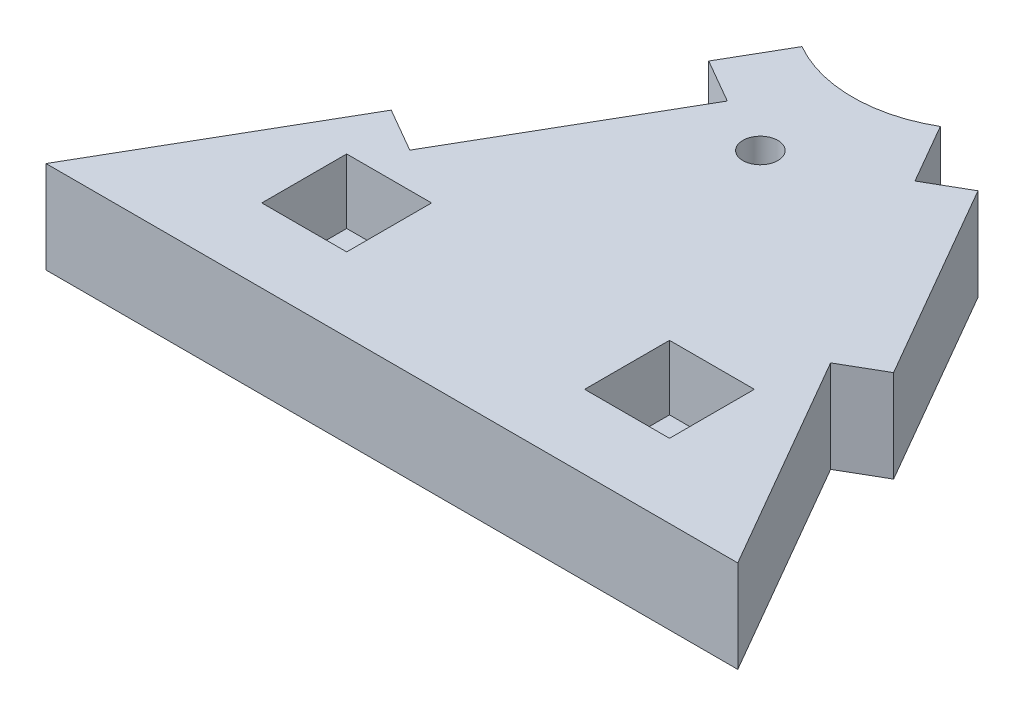
SolidWorks part; units mm, degrees
ref_plane "Front Plane" through (0, 0, 0) normal (0, 0, 1) x (1, 0, 0)
ref_plane "Top Plane" through (0, 0, 0) normal (0, 1, 0) x (1, 0, 0)
ref_plane "Right Plane" through (0, 0, 0) normal (1, 0, 0) x (0, 0, -1)
sketch "Sketch1" plane through (0, 0, 0) normal (0, 1, 0) x (1, 0, 0)
  line L0 (0, 0) -> (75, 0)
  line L1 (75, 0) -> (37.5, 64.9519)
  line L2 (37.5, 64.9519) -> (0, 0)
  dimension "D1" = 75
  dimension "D2" = 75
  dimension "D3" = 75
extrude "Boss-Extrude1" add sketch "Sketch1" along normal blind 10
sketch "Sketch2" plane through (0, 10, 0) normal (0, 1, 0) x (1, 0, 0)
  line L0 (37.5, 64.9519) -> (37.5, 0) construction
  line L1 (0, 0) -> (75, 0) construction
  line L2 (20, 0) -> (20, 34.641) construction
  line L6 (37.5, 64.9519) -> (0, 0) construction
  line L7 (50.4, 8) -> (50.4, 17.2)
  line L8 (15.4, 8) -> (24.6, 8)
  line L9 (15.4, 8) -> (15.4, 17.2)
  line L10 (15.4, 17.2) -> (24.6, 17.2)
  line L11 (24.6, 8) -> (24.6, 17.2)
  line L12 (15.4, 8) -> (24.6, 17.2) construction
  line L13 (15.4, 17.2) -> (24.6, 8) construction
  line L14 (59.6, 8) -> (50.4, 8)
  line L15 (59.6, 8) -> (59.6, 17.2)
  line L16 (59.6, 17.2) -> (50.4, 17.2)
  point P13 (20, 12.6)
  dimension "D1" = 17.5
  dimension "D3" = 8
  dimension "D4" = 9.2
  dimension "D5" = 9.2
extrude "Cut-Extrude1" cut sketch "Sketch2" against normal blind 7
sketch "Sketch3" plane through (0, 10, 0) normal (0, 1, 0) x (1, 0, 0)
  line L0 (18.75, 32.476) -> (26.3, 45.5529)
  line L1 (37.5, 64.9519) -> (0, 0) construction
  line L2 (26.3, 45.5529) -> (31.0631, 42.8029)
  line L3 (31.0631, 42.8029) -> (18.4631, 20.9791)
  line L4 (18.4631, 20.9791) -> (13.7, 23.7291)
  line L5 (13.7, 23.7291) -> (18.75, 32.476)
  dimension "D1" = 15.1
  dimension "D2" = 10.1
  dimension "D3" = 5.5
  dimension "D4" = 5.5
extrude "Cut-Extrude2" cut sketch "Sketch3" against normal through all
sketch "Sketch4" plane through (0, 10, 0) normal (0, 1, 0) x (1, 0, 0)
  line L0 (56.25, 32.476) -> (48.75, 45.4663)
  line L1 (75, 0) -> (37.5, 64.9519) construction
  line L2 (48.75, 45.4663) -> (53.0801, 47.9663)
  line L3 (53.0801, 47.9663) -> (65.5801, 26.3157)
  line L4 (65.5801, 26.3157) -> (61.25, 23.8157)
  line L5 (61.25, 23.8157) -> (56.25, 32.476)
  dimension "D1" = 15
  dimension "D2" = 10
  dimension "D3" = 5
  dimension "D4" = 5
extrude "Boss-Extrude2" add sketch "Sketch4" against normal blind 10
sketch "Sketch5" plane through (0, 10, 0) normal (0, 1, 0) x (1, 0, 0)
  line L0 (18.4631, 20.9791) -> (31.0631, 42.8029) construction
  line L1 (65.5801, 26.3157) -> (53.0801, 47.9663) construction
  line L2 (37.5, 64.9519) -> (37.5, 0) construction
  line L3 (0, 0) -> (75, 0) construction
  line L4 (37.5, 64.9519) -> (26.3, 45.5529) construction
  line L5 (48.75, 45.4663) -> (37.5, 64.9519) construction
  line L6 (30, 51.9615) -> (37.5, 64.9519)
  line L7 (37.5, 64.9519) -> (45, 51.9615)
  arc A0 (30.0694, 41.0817) -> (54.0776, 46.2387) centre (37.5, 64.9519) ccw construction
  circle A1 centre (37.5, 39.9519) radius 1.9
  arc A2 (30, 51.9615) -> (45, 51.9615) centre (37.5, 64.9519) ccw
  dimension "D1" = 25
  dimension "D2" = 3.8
  dimension "D3" = 15
extrude "Cut-Extrude3" cut sketch "Sketch5" against normal through all
